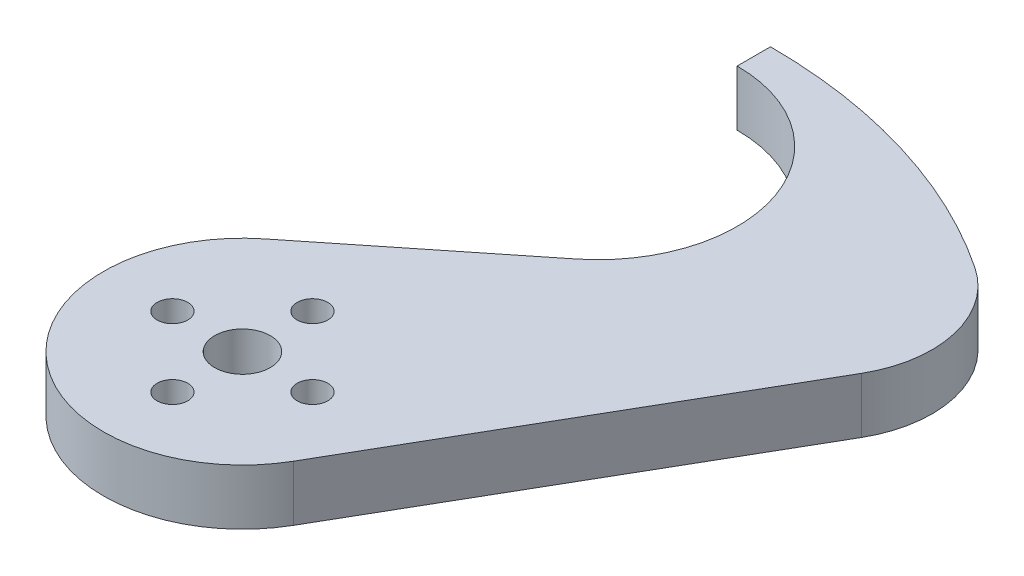
SolidWorks part; units mm, degrees
material "Pine"
ref_plane "Front Plane" through (0, 0, 0) normal (0, 0, 1) x (1, 0, 0)
ref_plane "Top Plane" through (0, 0, 0) normal (0, 1, 0) x (1, 0, 0)
ref_plane "Right Plane" through (0, 0, 0) normal (1, 0, 0) x (0, 0, -1)
sketch "Sketch1" plane through (0, 0, 0) normal (0, 1, 0) x (1, 0, 0)
  line L0 (13.7482, -7.9375) -> (42.8475, 42.4641)
  line L1 (9.9095, 28.2377) -> (-9.9095, 12.4023)
  line L2 (0, 40.64) -> (0, 0) construction
  line L3 (0, 60.325) -> (0, 56.515)
  circle A0 centre (0, 0) radius 3.175
  arc A1 (0, 60.325) -> (42.8475, 42.4641) centre (0, 0) cw
  arc A2 (-9.9095, 12.4023) -> (13.7482, -7.9375) centre (0, 0) ccw
  arc A3 (0, 56.515) -> (9.9095, 28.2377) centre (0, 40.64) cw
  dimension "D1" = 60.325
  dimension "D5" = 6.35
  dimension "D2" = 15.875
  dimension "D4" = 15.875
  dimension "D3" = 40.64
  dimension "D6" = 30
extrude "Boss-Extrude1" add sketch "Sketch1" along normal blind 6.35
sketch "Sketch2" plane through (0, 6.35, 0) normal (0, 1, 0) x (1, 0, 0)
  line L0 (0, 0) -> (8, 0) construction
  circle A0 centre (8, 0) radius 1.75
  dimension "D2" = 3.5
  dimension "D1" = 8
extrude "Cut-Extrude1" cut sketch "Sketch2" against normal through all
pattern_circular "CirPattern1" count 4 over 360 about axis through (0, 0, 0) along (0, 1, 0) of "Cut-Extrude1"
fillet "Fillet1" radius 12.7 1 edges at (42.8475, 3.175, -42.4641)
